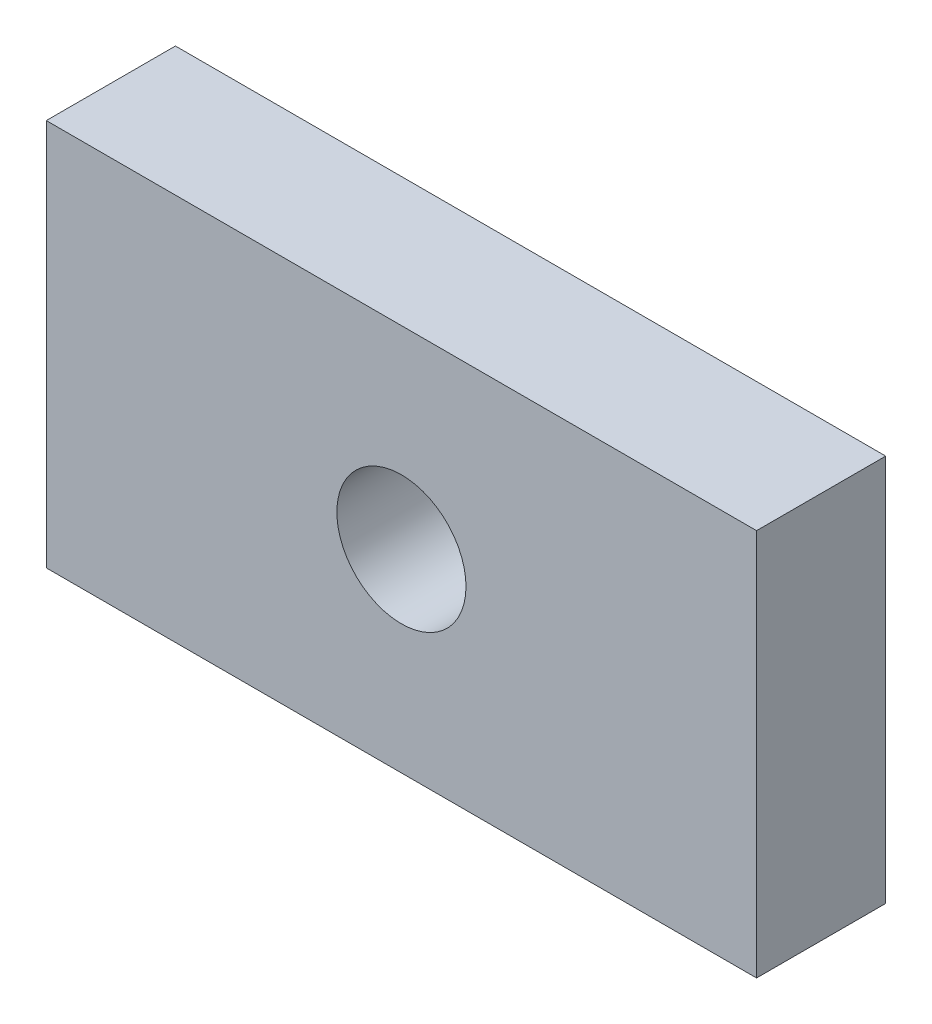
SolidWorks part; units mm, degrees
ref_plane "Front Plane" through (0, 0, 0) normal (0, 0, 1) x (1, 0, 0)
ref_plane "Top Plane" through (0, 0, 0) normal (0, 1, 0) x (1, 0, 0)
ref_plane "Right Plane" through (0, 0, 0) normal (1, 0, 0) x (0, 0, -1)
sketch "Sketch1" plane through (0, 0, 0) normal (0, 0, 1) x (1, 0, 0)
  line L1 (-69.85, 38.1) -> (69.85, 38.1)
  line L2 (-69.85, 38.1) -> (-69.85, -38.1)
  line L3 (-69.85, -38.1) -> (69.85, -38.1)
  line L4 (69.85, 38.1) -> (69.85, -38.1)
  circle A0 centre (0, 0) radius 12.7
  dimension "D5" = 25.4
  dimension "D1" = 139.7
  dimension "D2" = 76.2
  dimension "D3" = 69.85
  dimension "D4" = 38.1
extrude "Boss-Extrude2" add sketch "Sketch1" along normal blind 25.4
